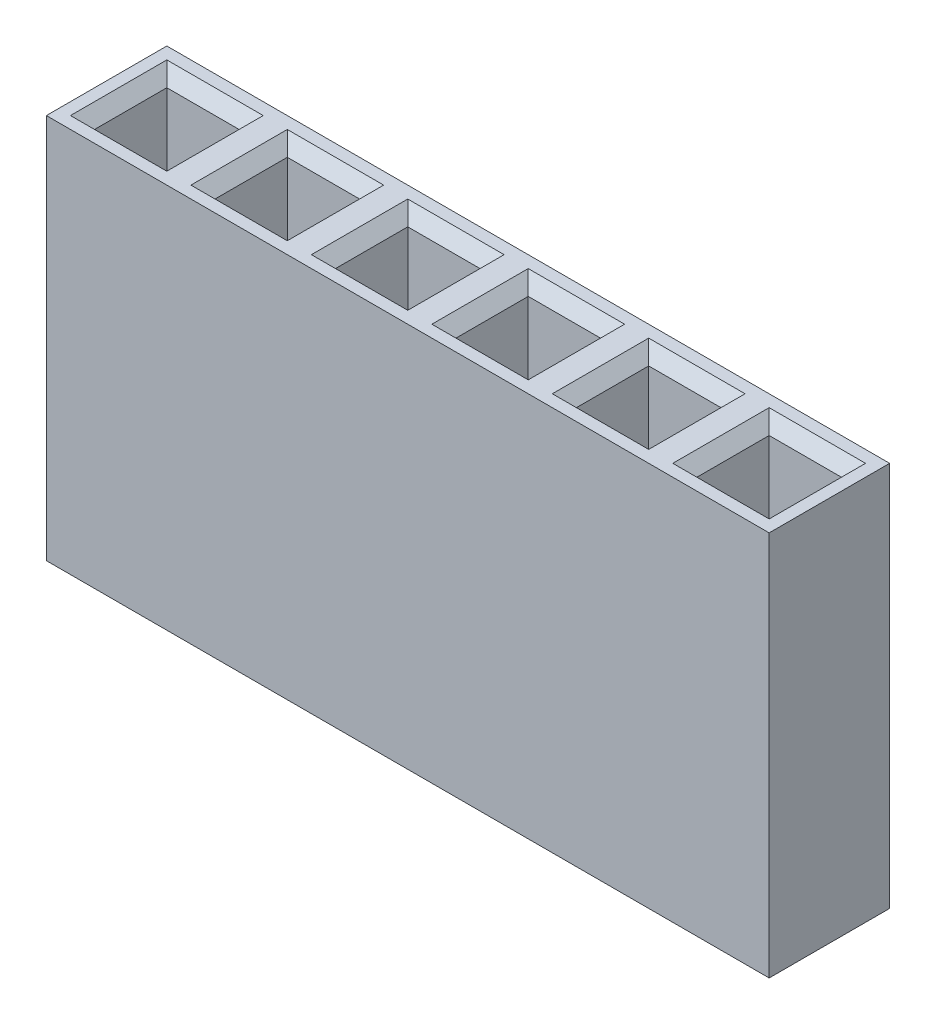
SolidWorks part; units mm, degrees
ref_plane "Front Plane" through (0, 0, 0) normal (0, 0, 1) x (1, 0, 0)
ref_plane "Top Plane" through (0, 0, 0) normal (0, 1, 0) x (1, 0, 0)
ref_plane "Right Plane" through (0, 0, 0) normal (1, 0, 0) x (0, 0, -1)
sketch "Sketch1" plane through (0, 0, 0) normal (0, 0, 1) x (1, 0, 0)
  line L1 (-1.25, -4) -> (1.25, -4)
  line L2 (-1.25, -4) -> (-1.25, 4)
  line L3 (-1.25, 4) -> (1.25, 4)
  line L4 (1.25, -4) -> (1.25, 4)
  line L5 (-1.25, -4) -> (1.25, 4) construction
  line L6 (-1.25, 4) -> (1.25, -4) construction
  point P0 (0, 0)
  dimension "D1" = 8
  dimension "D2" = 2.5
extrude "Boss-Extrude1" add sketch "Sketch1" along normal blind 2.5
sketch "Sketch2" plane through (0, 4, 0) normal (0, 1, 0) x (1, 0, 0)
  line L0 (0.75, -0.5) -> (-0.75, -0.5)
  line L1 (-0.75, -0.5) -> (-0.75, -2)
  line L2 (-0.75, -2) -> (0.75, -2)
  line L3 (0.75, -2) -> (0.75, -0.5)
  line L4 (1.25, 0) -> (-1.25, 0)
  line L5 (-1.25, 0) -> (-1.25, -2.5)
  line L6 (-1.25, -2.5) -> (1.25, -2.5)
  line L7 (1.25, -2.5) -> (1.25, 0)
  line L8 (1.25, 0) -> (-1.25, 0)
  line L9 (-1.25, 0) -> (-1.25, -2.5)
  line L10 (-1.25, -2.5) -> (1.25, -2.5)
  line L11 (1.25, -2.5) -> (1.25, 0)
  dimension "D1" = 0
  dimension "D2" = 0.5
extrude "Cut-Extrude2" cut sketch "Sketch2" against normal blind 7 contours L2 L3 L0 L1
chamfer "Chamfer3" distance 0.25 angle 45 4 edges at (0.75, 4, 1.25) (0, 4, 2) (-0.75, 4, 1.25) (0, 4, 0.5)
pattern_linear "LPattern2" count 6 spacing 2.5 along (1, 0, 0) of "Boss-Extrude1", "Cut-Extrude2", "Chamfer3"
